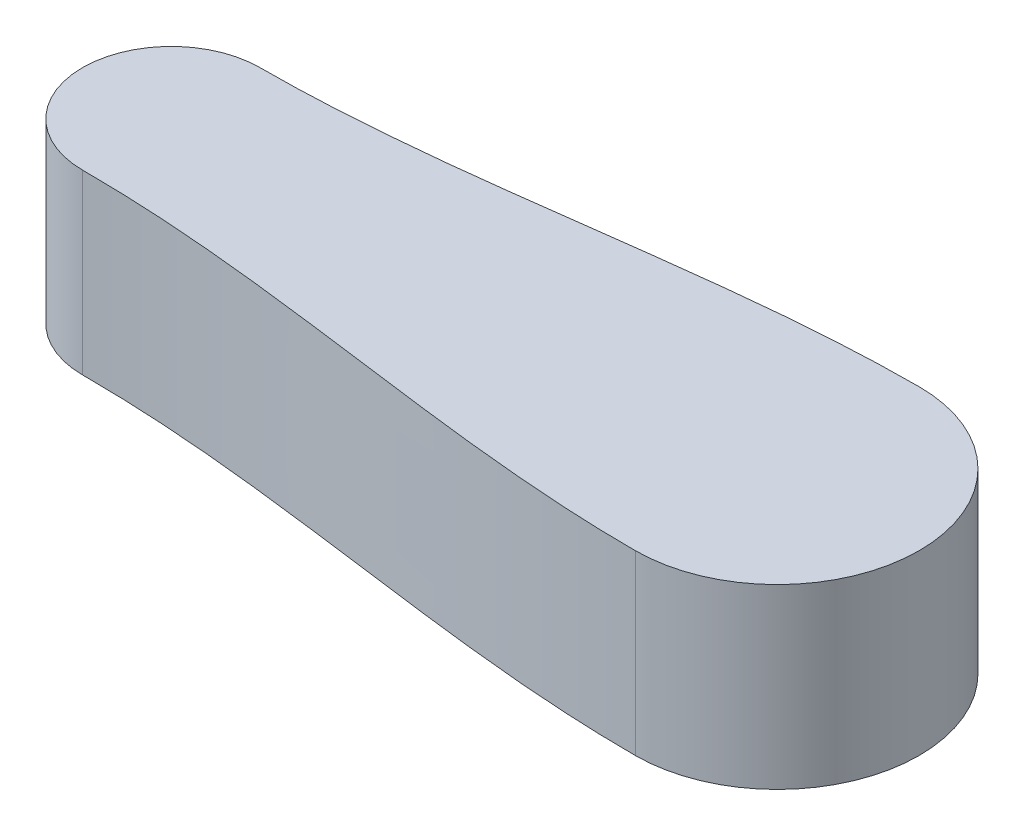
SolidWorks part; units mm, degrees
material "Silicon Rubber"
ref_plane "Front Plane" through (0, 0, 0) normal (0, 0, 1) x (1, 0, 0)
ref_plane "Top Plane" through (0, 0, 0) normal (0, 1, 0) x (1, 0, 0)
ref_plane "Right Plane" through (0, 0, 0) normal (1, 0, 0) x (0, 0, -1)
sketch "Sketch1" plane through (0, 0, 0) normal (0, 1, 0) x (1, 0, 0)
  line L0 (0, 25) -> (227, 25) construction
  line L1 (0, 0) -> (227, 0) construction
  line L2 (0, 0) -> (0, 50) construction
  line L3 (0, 50) -> (227, 50) construction
  line L4 (227, 0) -> (227, 50) construction
  arc A0 (25, 50) -> (25, 0) centre (25, 25) ccw
  arc A1 (195.775, -15) -> (195.775, 65) centre (195.775, 25) ccw
  spline S0 degree 3 poles (25, 50) (82.5808, 50) (138.6308, 65) (195.775, 65) knots 0 0 0 0 1 1 1 1
  spline S1 degree 3 poles (25, 0) (82.5808, 0) (138.6308, -15) (195.775, -15) knots 0 0 0 0 1 1 1 1
  dimension "D3" = 80
  dimension "D1" = 227
  dimension "D2" = 50
extrude "Boss-Extrude1" add sketch "Sketch1" along normal blind 50
sketch "Sketch2" plane through (0, 0, 0) normal (0, 0, 1) x (1, 0, 0)
  line L0 (0, 25) -> (171.5371, 25)
  line L1 (0, 50) -> (0, 0) construction
  line L3 (0, 25) -> (0, 50)
  line L4 (0, 50) -> (196.5371, 50)
  arc A0 (196.5371, 50) -> (171.5371, 25) centre (171.5371, 50) cw
sketch "Sketch3" plane through (0, 0, 0) normal (0, -1, 0) x (1, 0, 0)
  line L0 (162.775, -3) -> (162.775, -47) construction
  circle A0 centre (162.775, -3) radius 9.0897 construction
  circle A1 centre (162.775, -47) radius 9.0897 construction
  arc A2 (195.775, -65) -> (195.775, 15) centre (195.775, -25) ccw construction
  point P4 (162.775, -25)
  point P8 (235.775, -25)
  dimension "D1" = 44
  dimension "D3" = 18.1794
  dimension "D2" = 73
hole_wizard "M5 Tapped Hole1" positions "Sketch4" profile "Sketch5" tap size "M5" standard "ISO"
sketch "Sketch4" plane through (0, 0, 0) normal (0, -1, 0) x (-1, 0, 0)
  point P0 (-162.775, 3)
  point P3 (-162.775, 47)
sketch "Sketch5" plane through (162.775, 0, -3) normal (1, 0, 0) x (0, 0, -1)
  line L0 (0, 0) -> (0, 15.2618)
  line L1 (0, 15.2618) -> (2.1, 14)
  line L2 (2.1, 14) -> (2.1, 0)
  line L5 (2.1, 0) -> (0, 0)
  line L10 (0, 15.2618) -> (-2.1, 14) construction
  line L11 (0, -6.35) -> (0, 107.95) construction
  dimension "Tap Drill Dia." = 4.2
  dimension "Tap Drill Depth" = 14
  dimension "Drill Angle" = 118
